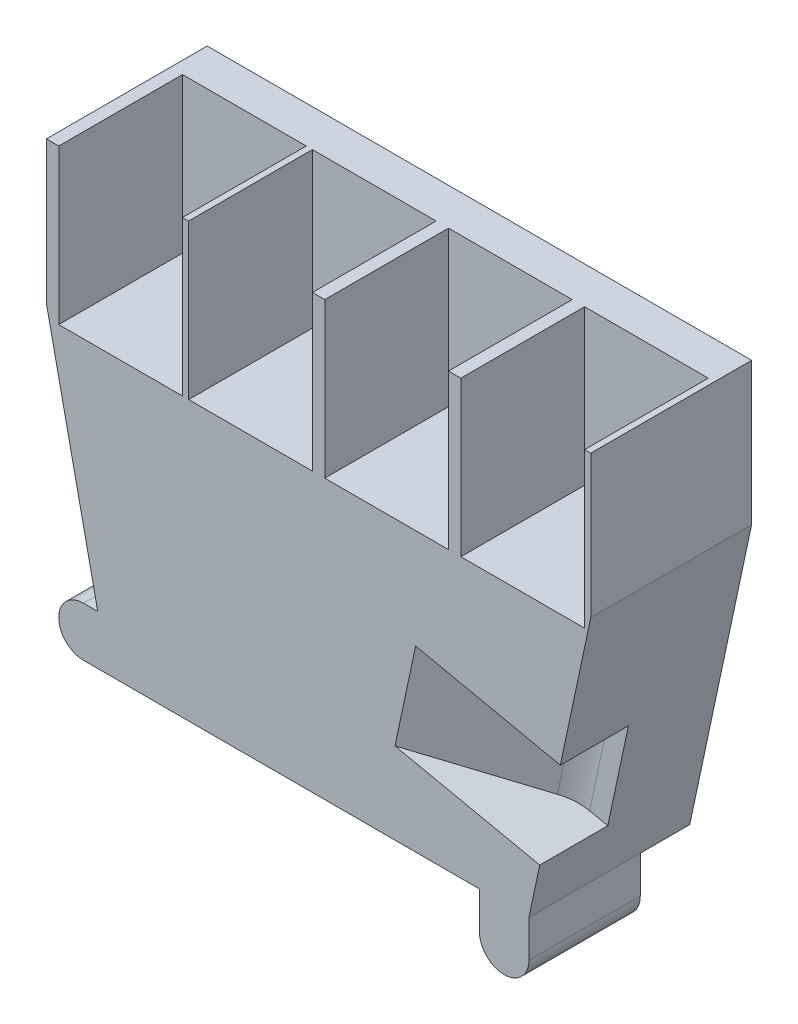
SolidWorks part; units mm, degrees
ref_plane "Front" through (0, 0, 0) normal (0, 0, 1) x (1, 0, 0)
ref_plane "Top" through (0, 0, 0) normal (0, 1, 0) x (1, 0, 0)
ref_plane "Right" through (0, 0, 0) normal (1, 0, 0) x (0, 0, -1)
sketch "草图1" plane through (0, 0, 0) normal (0, 0, 1) x (1, 0, 0)
  line L0 (-34, -24) -> (34, -24)
  line L1 (-44, 46) -> (44, 46)
  line L2 (-44, 46) -> (-44, 23)
  line L4 (44, 46) -> (44, 23)
  line L5 (-66.7553, 0) -> (86.3051, 0) construction
  line L8 (-44, 23) -> (-34, -24)
  line L9 (-44, 23) -> (56.7889, 23) construction
  line L10 (34, -24) -> (44, 23)
  dimension "D1" = 88
  dimension "D3" = 44
  dimension "D4" = 68
  dimension "D5" = 34
  dimension "D6" = 24
extrude "凸台-拉伸1" add sketch "草图1" along normal blind 26
sketch "草图4" plane through (0, 46, 0) normal (0, 1, 0) x (1, 0, 0)
  line L0 (44, -26) -> (-44, -26) construction
  line L1 (43, -26) -> (23, -26)
  line L2 (43, -26) -> (43, -6)
  line L3 (43, -6) -> (23, -6)
  line L4 (23, -26) -> (23, -6)
  line L5 (44, -26) -> (44, 0) construction
  line L6 (21, -26) -> (1, -26)
  line L7 (21, -26) -> (21, -6)
  line L8 (21, -6) -> (1, -6)
  line L9 (1, -26) -> (1, -6)
  line L10 (-1, -26) -> (-21, -26)
  line L11 (-1, -26) -> (-1, -6)
  line L12 (-1, -6) -> (-21, -6)
  line L13 (-21, -26) -> (-21, -6)
  line L14 (-22, -26) -> (-42, -26)
  line L15 (-22, -26) -> (-22, -6)
  line L16 (-22, -6) -> (-42, -6)
  line L17 (-42, -26) -> (-42, -6)
  dimension "D1" = 20
  dimension "D2" = 21
  dimension "D3" = 20
  dimension "D4" = 20
  dimension "D5" = 20
  dimension "D6" = 2
  dimension "D7" = 2
  dimension "D8" = 20
  dimension "D9" = 20
  dimension "D10" = 20
  dimension "D11" = 21
  dimension "D12" = 20
extrude "切除-拉伸5" cut sketch "草图4" against normal blind 25
sketch "草图6" plane through (37.4127, -7.9602, 0) normal (0.9781, -0.2081, 0) x (0, 0, -1)
  line L0 (0, 0) -> (-26, 0)
  line L1 (-26, -16.3989) -> (-26, 31.6532) construction
sketch3d "3D草图6"
  line L0 (37.4127, -7.9602, 0) -> (37.4127, -7.9602, 26) construction
  line L2 (37.4127, -7.9602, 26) -> (26.6536, -5.671, 25.9966) construction
  line L3 (34.4784, -7.3358, 14.9991) -> (44.8243, -9.5371, 14.9991)
  line L4 (34.4784, -7.3358, 29) -> (44.8243, -9.5371, 29)
  line L5 (44.8243, -9.5371, 29) -> (44.8243, -9.5371, 14.9991)
  line L6 (26.6536, -5.671, 22.9991) -> (26.6536, -5.671, 29)
  line L7 (26.6536, -5.671, 29) -> (34.4784, -7.3358, 29)
  arc A0 (34.4784, -7.3358, 14.9991) -> (26.6536, -5.671, 22.9991) centre (34.4784, -7.3358, 22.9991) ccw
  point P2 (36.1433, 0.489, 22.9991)
  dimension "D1" = 3
  dimension "D2" = 3
extrude "切除-拉伸6" cut sketch "3D草图6" along direction (0.2081, 0.9781, 0) on the side against the normal mid plane 16
sketch "草图11" plane through (-1.6649, -7.8248, 0) normal (0.2081, 0.9781, 0) x (0.9781, -0.2081, 0)
  line L0 (-28.261, -26) -> (38.2502, -26) construction
  line L1 (38.2502, 0) -> (38.2502, -26) construction
  line L2 (24.5567, -20) -> (31.2008, -16.1005) construction
  line L3 (31.2008, -16.1005) -> (14.3336, -26)
  line L4 (14.3336, -26) -> (32.6666, -30.5713)
  line L5 (35.2502, -15) -> (38.2502, -14.9991)
  line L6 (38.2502, -14.9991) -> (40.4608, -16.9296)
  arc A0 (32.6666, -30.5713) -> (40.4608, -16.9296) centre (35.2502, -23) ccw
  arc A1 (35.2502, -15) -> (31.2008, -16.1005) centre (35.2502, -23) ccw
  dimension "D1" = 3
  dimension "D2" = 3
extrude "切除-拉伸8" cut sketch "草图11" along normal blind 16
sketch "草图12" plane through (0, 0, 0) normal (0, 0, -1) x (-1, 0, 0)
  line L1 (-34, -24) -> (-26, -24)
  line L2 (-34, -24) -> (-34, -34)
  line L3 (-34, -34) -> (-26, -34)
  line L4 (-26, -24) -> (-26, -34)
  line L9 (34, -24) -> (38, -24)
  line L10 (34, -24) -> (34, -16)
  line L11 (34, -16) -> (38, -16)
  arc A0 (38, -24) -> (38, -16) centre (38, -20) ccw
  dimension "D1" = 8
  dimension "D2" = 10
extrude "凸台-拉伸2" add sketch "草图12" against normal blind 26
sketch "草图13" plane through (0, 0, 0) normal (0, 0, -1) x (-1, 0, 0)
  line L2 (-34, -30) -> (-34, -35.7722)
  line L3 (-34, -35.7722) -> (-26, -35.7722)
  line L4 (-26, -30) -> (-26, -35.7722)
  line L6 (26, -30) -> (26, -35.7722)
  line L7 (26, -35.7722) -> (34, -35.7722)
  line L8 (34, -30) -> (34, -35.7722)
  arc A0 (-34, -30) -> (-26, -30) centre (-30, -30) ccw
  arc A1 (26, -30) -> (34, -30) centre (30, -30) ccw
extrude "切除-拉伸9" cut sketch "草图13" against normal blind 26
sketch "草图14" plane through (34, 0, 0) normal (1, 0, 0) x (0, 0, -1)
  line L1 (0, -24) -> (-8, -24)
  line L2 (0, -24) -> (0, -36.8631)
  line L3 (0, -36.8631) -> (-8, -36.8631)
  line L4 (-8, -24) -> (-8, -36.8631)
  dimension "D1" = 8
extrude "切除-拉伸10" cut sketch "草图14" against normal through all
